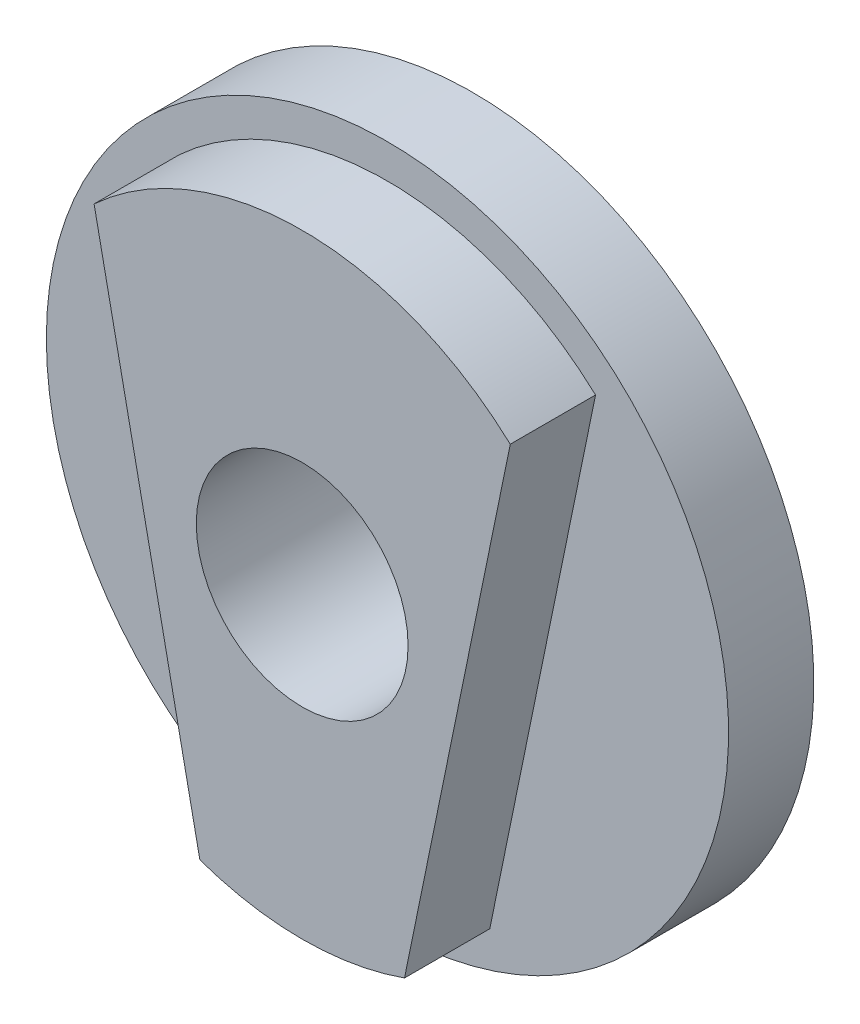
SolidWorks part; units mm, degrees
ref_plane "Alzado" through (0, 0, 0) normal (0, 0, 1) x (1, 0, 0)
ref_plane "Planta" through (0, 0, 0) normal (0, 1, 0) x (1, 0, 0)
ref_plane "Vista lateral" through (0, 0, 0) normal (1, 0, 0) x (0, 0, -1)
ref_plane "Plane1" through (0, 0, 0) normal (0, -1, 0) x (1, 0, 0)
sketch "Sketch1" plane through (0, 0, 0) normal (0, -1, 0) x (1, 0, 0)
  line L0 (1, 0.425) -> (0, 0.425)
  line L1 (0, 0.425) -> (0, 0.175)
  line L2 (0, 0.175) -> (1, 0.175)
  line L3 (1, 0.175) -> (1, 0.425)
  line L4 (0, 0.425) -> (0, 0.175) construction
  dimension "D1" = 1
  dimension "D2" = 0.25
revolve "Revolve1" add sketch "Sketch1" angle 360 about L4
sketch "Sketch2" plane through (0, 0, 0.425) normal (0, 0, 1) x (1, 0, 0)
  line L0 (-1000, 0) -> (49000, 0) construction
  line L1 (0.3, -1000.1183) -> (0.3, 48999.8817) construction
  line L2 (0, -1000) -> (0, 49000) construction
  line L3 (0.3, -0.8485) -> (10054.1961, 48977.914) construction
  line L4 (0.61, 0.6617) -> (0.3, -0.8485)
  line L5 (-0.61, 0.6617) -> (-0.3, -0.8485)
  circle A0 centre (0, 0) radius 0.9 construction
  arc A1 (0.61, 0.6617) -> (-0.61, 0.6617) centre (0, 0) ccw
  arc A4 (-0.3, -0.8485) -> (0.3, -0.8485) centre (0, 0) ccw
  point P6 (0.3, -0.8485)
  dimension "D1" = 0.3
  dimension "D2" = 1.8
  dimension "D3" = 11.6
extrude "Boss-Extrude1" add sketch "Sketch2" along normal blind 0.25
sketch "Sketch3" plane through (0, 0, 0) normal (0, 0, 1) x (1, 0, 0)
  circle A0 centre (0, 0) radius 0.3105
  dimension "D1" = 0.621
extrude "Cut-Extrude1" cut sketch "Sketch3" along normal up to next
